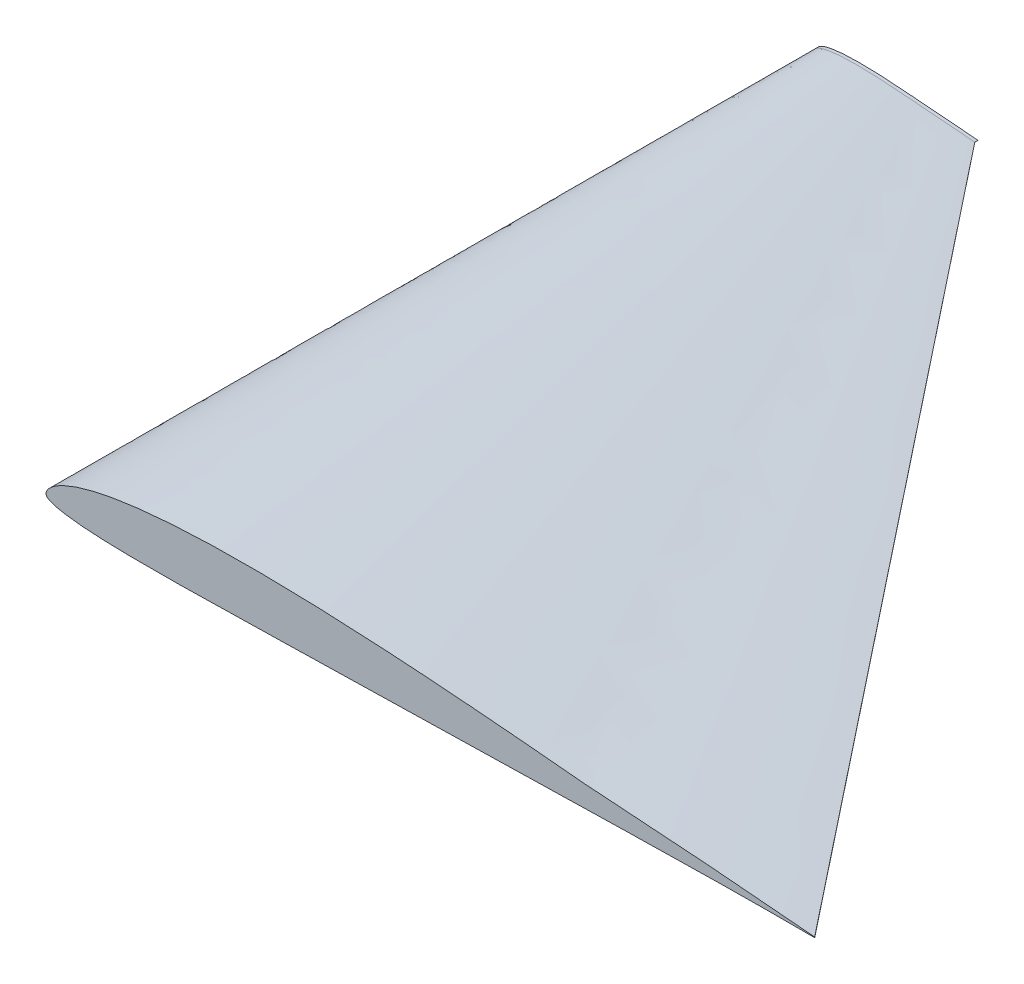
SolidWorks part; units mm, degrees
ref_plane "Front Plane" through (0, 0, 0) normal (0, 0, 1) x (1, 0, 0)
ref_plane "Top Plane" through (0, 0, 0) normal (0, 1, 0) x (1, 0, 0)
ref_plane "Right Plane" through (0, 0, 0) normal (1, 0, 0) x (0, 0, -1)
curve "Curve1"
  spline degree 3 poles (25.4, 0.0107, 0) (25.3506, 0.0152, 0) (25.2009, 0.0289, 0) (24.9376, 0.0531, 0) (24.6076, 0.082, 0) (24.2616, 0.1124, 0) (23.9125, 0.1431, 0) (23.5625, 0.1725, 0) (23.212, 0.2019, 0) (22.8613, 0.2307, 0) (22.5105, 0.2591, 0) (22.1596, 0.2869, 0) (21.8089, 0.314, 0) (21.4582, 0.3409, 0) (21.1077, 0.367, 0) (20.7573, 0.3928, 0) (20.407, 0.4182, 0) (20.0568, 0.4428, 0) (19.7068, 0.4673, 0) (19.3568, 0.4911, 0) (19.0069, 0.5145, 0) (18.6571, 0.5374, 0) (18.3335, 0.5583, 0) (18.0818, 0.5739, 0) (17.9246, 0.5843, 0) (17.8356, 0.5888, 0) (17.7472, 0.5983, 0) (17.5613, 0.6156, 0) (17.278, 0.6431, 0) (16.98, 0.6709, 0) (16.7137, 0.6956, 0) (16.4751, 0.7176, 0) (16.176, 0.7447, 0) (15.8267, 0.776, 0) (15.4701, 0.8073, 0) (15.1145, 0.838, 0) (14.7793, 0.8663, 0) (14.4495, 0.8936, 0) (14.1621, 0.9169, 0) (13.925, 0.9358, 0) (13.6642, 0.9563, 0) (13.3619, 0.9794, 0) (13.0103, 1.0056, 0) (12.659, 1.031, 0) (12.3077, 1.0554, 0) (11.9565, 1.0789, 0) (11.6054, 1.1014, 0) (11.2544, 1.1228, 0) (10.9034, 1.1432, 0) (10.5525, 1.1624, 0) (10.2016, 1.1803, 0) (9.8507, 1.197, 0) (9.5, 1.2123, 0) (9.1492, 1.2263, 0) (8.7986, 1.2386, 0) (8.448, 1.2494, 0) (8.0977, 1.2585, 0) (7.7474, 1.2658, 0) (7.3974, 1.2711, 0) (7.0475, 1.2745, 0) (6.6979, 1.2756, 0) (6.3485, 1.2744, 0) (5.9995, 1.2706, 0) (5.6509, 1.2642, 0) (5.3028, 1.2548, 0) (4.9554, 1.2422, 0) (4.6087, 1.2261, 0) (4.2629, 1.2062, 0) (3.9183, 1.1823, 0) (3.5751, 1.1536, 0) (3.2336, 1.12, 0) (2.8944, 1.0807, 0) (2.5581, 1.0351, 0) (2.2254, 0.9824, 0) (1.8975, 0.9214, 0) (1.5762, 0.8511, 0) (1.2643, 0.7698, 0) (0.9677, 0.6771, 0) (0.6972, 0.5737, 0) (0.4689, 0.4653, 0) (0.2948, 0.361, 0) (0.1747, 0.2696, 0) (0.0967, 0.1939, 0) (0.0471, 0.1311, 0) (0.0171, 0.0777, 0) (0.0019, 0.0319, 0) (-0.0016, -0.0085, 0) (0.0071, -0.0466, 0) (0.0322, -0.0832, 0) (0.0764, -0.1158, 0) (0.1405, -0.1489, 0) (0.2348, -0.1846, 0) (0.3747, -0.2244, 0) (0.5727, -0.265, 0) (0.8268, -0.3029, 0) (1.1218, -0.3343, 0) (1.4394, -0.3584, 0) (1.7684, -0.3763, 0) (2.1036, -0.389, 0) (2.4428, -0.3976, 0) (2.7846, -0.4031, 0) (3.1285, -0.4061, 0) (3.4739, -0.407, 0) (3.8205, -0.4061, 0) (4.168, -0.4035, 0) (4.5164, -0.3997, 0) (4.8654, -0.3948, 0) (5.2151, -0.389, 0) (5.5654, -0.3825, 0) (5.9165, -0.3755, 0) (6.2684, -0.368, 0) (6.621, -0.3604, 0) (6.9745, -0.3524, 0) (7.3287, -0.3442, 0) (7.6835, -0.336, 0) (8.039, -0.3276, 0) (8.3948, -0.3192, 0) (8.7511, -0.3108, 0) (9.1077, -0.3024, 0) (9.4646, -0.2939, 0) (9.8219, -0.2855, 0) (10.1795, -0.2771, 0) (10.5373, -0.2687, 0) (10.8952, -0.2603, 0) (11.2527, -0.252, 0) (11.6101, -0.2438, 0) (11.9672, -0.2355, 0) (12.3241, -0.2274, 0) (12.6807, -0.2193, 0) (13.0371, -0.2114, 0) (13.3934, -0.2033, 0) (13.6949, -0.1966, 0) (13.9592, -0.1908, 0) (14.1921, -0.1856, 0) (14.4749, -0.1792, 0) (14.7878, -0.1723, 0) (15.131, -0.1647, 0) (15.4754, -0.1569, 0) (15.8234, -0.1492, 0) (16.1349, -0.1423, 0) (16.4075, -0.1363, 0) (16.6379, -0.1313, 0) (16.9029, -0.1255, 0) (17.2072, -0.1189, 0) (17.4885, -0.1128, 0) (17.6791, -0.1088, 0) (17.7715, -0.1068, 0) (17.8501, -0.1053, 0) (18.0096, -0.1018, 0) (18.269, -0.0964, 0) (18.61, -0.0893, 0) (18.9621, -0.082, 0) (19.3141, -0.0749, 0) (19.666, -0.0678, 0) (20.0179, -0.0609, 0) (20.3698, -0.054, 0) (20.7219, -0.0473, 0) (21.074, -0.0408, 0) (21.4262, -0.0348, 0) (21.7784, -0.0292, 0) (22.1308, -0.0242, 0) (22.4832, -0.0197, 0) (22.8357, -0.0157, 0) (23.1883, -0.0125, 0) (23.5408, -0.0098, 0) (23.8935, -0.008, 0) (24.246, -0.0071, 0) (24.5963, -0.007, 0) (24.9308, -0.0084, 0) (25.198, -0.0096, 0) (25.3499, -0.0104, 0) (25.4, -0.0107, 0) knots 0 0 0 0 0.002901 0.008799 0.015478 0.022288 0.029131 0.035985 0.042847 0.049714 0.056581 0.063448 0.070313 0.077171 0.084031 0.090885 0.097737 0.104584 0.111432 0.118275 0.125116 0.131954 0.138793 0.144098 0.146709 0.148014 0.149313 0.151911 0.158945 0.165974 0.169425 0.174599 0.18 0.186998 0.195126 0.200949 0.20789 0.214818 0.220317 0.224762 0.228741 0.235631 0.242503 0.249376 0.256249 0.263115 0.269975 0.276837 0.283698 0.290553 0.297409 0.304262 0.311112 0.317958 0.324805 0.331647 0.338484 0.345319 0.352149 0.358974 0.365797 0.372613 0.37942 0.386225 0.393018 0.399801 0.406576 0.413331 0.420073 0.426793 0.433487 0.440154 0.446776 0.453353 0.459862 0.466294 0.472602 0.478718 0.484477 0.489534 0.493496 0.496331 0.498346 0.499841 0.500999 0.501915 0.502649 0.503345 0.504158 0.505185 0.506526 0.508376 0.511074 0.515031 0.520197 0.526109 0.532386 0.538838 0.545393 0.552019 0.558693 0.565404 0.572145 0.578909 0.585689 0.592488 0.599298 0.60612 0.612956 0.619809 0.626673 0.633554 0.640451 0.647364 0.654291 0.661227 0.668172 0.675126 0.682086 0.689049 0.69602 0.703 0.709987 0.71697 0.723948 0.73092 0.73789 0.744856 0.751814 0.758769 0.765721 0.77267 0.776424 0.78119 0.786305 0.792978 0.79951 0.806399 0.81314 0.819881 0.824633 0.829103 0.833367 0.840145 0.84692 0.849831 0.851305 0.852333 0.85443 0.860642 0.867519 0.87439 0.881257 0.888123 0.894989 0.901857 0.908727 0.915597 0.922469 0.929344 0.936217 0.943092 0.949972 0.956848 0.963729 0.970609 0.97749 0.984361 0.991109 0.997067 1 1 1 1
sketch "Sketch2" plane through (0, 0, 0) normal (0, 0, 1) x (1, 0, 0)
  line L0 (64.7182, -2.4991) -> (64.7182, -2.5635)
  line L1 (127, 0.0536) -> (127, -0.0536)
  line L2 (0, 0) -> (127, 0.0536) construction
  spline S1 degree 3 poles (609.6, 0.2573) (608.4153, 0.3652) (604.8219, 0.6927) (598.502, 1.2752) (590.5825, 1.9674) (582.2775, 2.6983) (573.9006, 3.4339) (565.4998, 4.1403) (557.089, 4.8463) (548.6715, 5.5358) (540.2515, 6.218) (531.8311, 6.8852) (523.413, 7.5348) (514.9974, 8.1818) (506.5852, 8.8084) (498.1747, 9.4281) (489.7686, 10.036) (481.3637, 10.627) (472.9627, 11.2149) (464.5629, 11.7866) (456.1664, 12.3471) (447.7708, 12.8983) (440.0032, 13.3997) (433.9644, 13.7741) (430.1915, 14.0231) (428.0555, 14.1319) (425.9338, 14.3593) (421.4712, 14.7735) (414.6712, 15.4343) (407.5204, 16.1015) (401.1285, 16.6942) (395.4014, 17.222) (388.2248, 17.8734) (379.8411, 18.6251) (371.2834, 19.3759) (362.7481, 20.1109) (354.702, 20.791) (346.7874, 21.4473) (339.8916, 22.0057) (334.2002, 22.4585) (327.9397, 22.9514) (320.686, 23.506) (312.248, 24.1341) (303.8155, 24.7432) (292.5775, 25.5244) (281.3407, 26.2607) (270.1062, 26.9482) (261.6823, 27.4364) (250.4535, 28.0507) (239.2258, 28.6059) (227.9988, 29.096) (219.5815, 29.4314) (211.1661, 29.7272) (202.7531, 29.9856) (194.3438, 30.2035) (185.9386, 30.3795) (177.5376, 30.5072) (169.1408, 30.5885) (160.7491, 30.6149) (152.3646, 30.5852) (143.9885, 30.4949) (135.6226, 30.341) (127.2682, 30.115) (118.9286, 29.8125) (110.6079, 29.4273) (102.3088, 28.9496) (94.0382, 28.3746) (85.8017, 27.6874) (77.6067, 26.8808) (69.4667, 25.9361) (61.3935, 24.8424) (53.4108, 23.5771) (45.5411, 22.1146) (37.8288, 20.426) (30.344, 18.4761) (23.2242, 16.2498) (16.7336, 13.7685) (11.2526, 11.1662) (7.0744, 8.6642) (4.192, 6.4716) (2.3207, 4.6541) (1.1306, 3.147) (0.4097, 1.8653) (0.0445, 0.7644) (-0.0394, -0.2051) (0.1701, -1.1192) (0.7717, -1.9972) (1.8329, -2.7786) (3.3717, -3.5735) (5.6341, -4.4311) (8.992, -5.3852) (13.7441, -6.3602) (19.844, -7.2691) (26.9221, -8.0223) (34.5451, -8.6019) (42.4418, -9.0313) (50.4869, -9.3361) (58.6261, -9.543) (66.8307, -9.6749) (75.0831, -9.7467) (83.3728, -9.7692) (91.6908, -9.7458) (100.0329, -9.6848) (108.3931, -9.5935) (116.7701, -9.4746) (125.1618, -9.3356) (133.5708, -9.1799) (141.9971, -9.0125) (150.4416, -8.8321) (158.9043, -8.6491) (167.3869, -8.4567) (175.8879, -8.2608) (187.2521, -7.9967) (198.6327, -7.7272) (210.0269, -7.4583) (218.5851, -7.2569) (227.1506, -7.0539) (235.7244, -6.8527) (244.3077, -6.6496) (252.896, -6.449) (261.4836, -6.2483) (270.0654, -6.0486) (278.6417, -5.8521) (287.2128, -5.6526) (295.7783, -5.4585) (304.3375, -5.264) (312.891, -5.0728) (321.4408, -4.88) (328.6786, -4.7192) (337.1174, -4.5324) (345.4426, -4.3447) (354.9071, -4.135) (363.1446, -3.9522) (371.4102, -3.7664) (379.7615, -3.5814) (387.2366, -3.4158) (393.7811, -3.2715) (399.3097, -3.1512) (405.6693, -3.0117) (412.9735, -2.8543) (419.723, -2.7081) (424.2983, -2.6117) (426.5172, -2.5634) (428.4027, -2.5274) (432.2303, -2.443) (438.4564, -2.3133) (446.6397, -2.1424) (455.0912, -1.9684) (463.5382, -1.7984) (471.983, -1.6281) (480.4288, -1.4625) (488.876, -1.2962) (497.3253, -1.1358) (505.7757, -0.9782) (514.2284, -0.8363) (525.5014, -0.6571) (536.7782, -0.5043) (548.0561, -0.376) (556.518, -0.299) (564.9803, -0.2347) (573.4446, -0.1921) (581.9048, -0.1708) (590.3111, -0.1673) (598.3385, -0.2004) (604.7515, -0.2296) (608.3973, -0.2504) (609.6, -0.2573) knots 0 0 0 0 0.002901 0.008799 0.015478 0.022288 0.029131 0.035985 0.042847 0.049714 0.056581 0.063448 0.070313 0.077171 0.084031 0.090885 0.097737 0.104584 0.111432 0.118275 0.125116 0.131954 0.138793 0.144098 0.146709 0.148014 0.149313 0.151911 0.158945 0.165974 0.169425 0.174599 0.18 0.186998 0.195126 0.200949 0.20789 0.214818 0.220317 0.224762 0.228741 0.235631 0.242503 0.249376 0.256249 0.269975 0.276837 0.283698 0.290553 0.304262 0.311112 0.317958 0.324805 0.331647 0.338484 0.345319 0.352149 0.358974 0.365797 0.372613 0.37942 0.386225 0.393018 0.399801 0.406576 0.413331 0.420073 0.426793 0.433487 0.440154 0.446776 0.453353 0.459862 0.466294 0.472602 0.478718 0.484477 0.489534 0.493496 0.496331 0.498346 0.499841 0.500999 0.501915 0.502649 0.503345 0.504158 0.505185 0.506526 0.508376 0.511074 0.515031 0.520197 0.526109 0.532386 0.538838 0.545393 0.552019 0.558693 0.565404 0.572145 0.578909 0.585689 0.592488 0.599298 0.60612 0.612956 0.619809 0.626673 0.633554 0.640451 0.647364 0.654291 0.668172 0.675126 0.682086 0.689049 0.69602 0.703 0.709987 0.71697 0.723948 0.73092 0.73789 0.744856 0.751814 0.758769 0.765721 0.77267 0.776424 0.786305 0.792978 0.79951 0.806399 0.81314 0.819881 0.824633 0.829103 0.833367 0.840145 0.84692 0.849831 0.851305 0.852333 0.85443 0.860642 0.867519 0.87439 0.881257 0.888123 0.894989 0.901857 0.908727 0.915597 0.922469 0.929344 0.943092 0.949972 0.956848 0.963729 0.970609 0.97749 0.984361 0.991109 0.997067 1 1 1 1
  spline S2 degree 3 poles (127, 0.0536) (126.7532, 0.0761) (126.0046, 0.1443) (124.6879, 0.2657) (123.038, 0.4099) (121.3078, 0.5622) (119.5626, 0.7154) (117.8125, 0.8626) (116.0602, 1.0096) (114.3066, 1.1533) (112.5524, 1.2954) (110.7981, 1.4344) (109.0444, 1.5698) (107.2911, 1.7045) (105.5386, 1.8351) (103.7864, 1.9642) (102.0351, 2.0908) (100.2841, 2.214) (98.5339, 2.3364) (96.7839, 2.4555) (95.0347, 2.5723) (93.2856, 2.6871) (91.6673, 2.7916) (90.4092, 2.8696) (89.6232, 2.9215) (89.1782, 2.9441) (88.7362, 2.9915) (87.8065, 3.0778) (86.3898, 3.2155) (84.9001, 3.3545) (83.5684, 3.478) (82.3753, 3.5879) (80.8802, 3.7236) (79.1336, 3.8802) (77.3507, 4.0366) (75.5725, 4.1898) (73.8963, 4.3315) (72.2474, 4.4682) (70.8107, 4.5845) (69.625, 4.6789) (68.3208, 4.7815) (66.8096, 4.8971) (65.0517, 5.0279) (63.2949, 5.1548) (60.9536, 5.3176) (58.6126, 5.471) (56.2721, 5.6142) (54.5172, 5.7159) (52.1778, 5.8439) (49.8387, 5.9596) (47.4998, 6.0617) (45.7461, 6.1315) (43.9929, 6.1932) (42.2402, 6.247) (40.4883, 6.2924) (38.7372, 6.3291) (36.987, 6.3557) (35.2377, 6.3726) (33.4894, 6.3781) (31.7426, 6.3719) (29.9976, 6.3531) (28.2547, 6.321) (26.5142, 6.274) (24.7768, 6.2109) (23.0433, 6.1307) (21.3143, 6.0312) (19.5913, 5.9114) (17.8753, 5.7682) (16.1681, 5.6002) (14.4722, 5.4034) (12.7903, 5.1755) (11.1272, 4.9119) (9.4877, 4.6072) (7.881, 4.2554) (6.3217, 3.8492) (4.8384, 3.3854) (3.4862, 2.8684) (2.3443, 2.3263) (1.4738, 1.805) (0.8733, 1.3482) (0.4835, 0.9696) (0.2355, 0.6556) (0.0854, 0.3886) (0.0093, 0.1593) (-0.0082, -0.0427) (0.0354, -0.2332) (0.1608, -0.4161) (0.3818, -0.5789) (0.7024, -0.7445) (1.1738, -0.9231) (1.8733, -1.1219) (2.8634, -1.3251) (4.1342, -1.5144) (5.6088, -1.6713) (7.1969, -1.7921) (8.842, -1.8815) (10.5181, -1.945) (12.2138, -1.9881) (13.9231, -2.0156) (15.6423, -2.0306) (17.3693, -2.0352) (19.1023, -2.0304) (20.8402, -2.0177) (22.5819, -1.9987) (24.3271, -1.9739) (26.0754, -1.9449) (27.8272, -1.9125) (29.5827, -1.8776) (31.342, -1.84) (33.1051, -1.8019) (34.8723, -1.7618) (36.6433, -1.721) (39.0109, -1.666) (41.3818, -1.6098) (43.7556, -1.5538) (45.5386, -1.5118) (47.323, -1.4696) (49.1093, -1.4276) (50.8974, -1.3853) (52.6867, -1.3435) (54.4758, -1.3017) (56.2636, -1.2601) (58.0503, -1.2192) (59.836, -1.1776) (61.6205, -1.1372) (63.4036, -1.0967) (65.1856, -1.0568) (66.9668, -1.0167) (68.4747, -0.9832) (70.2328, -0.9443) (71.9672, -0.9051) (73.939, -0.8615) (75.6551, -0.8234) (77.3771, -0.7847) (79.117, -0.7461) (80.6743, -0.7116) (82.0377, -0.6816) (83.1895, -0.6565) (84.5144, -0.6274) (86.0361, -0.5947) (87.4423, -0.5642) (88.3955, -0.5441) (88.8577, -0.534) (89.2506, -0.5265) (90.048, -0.509) (91.3451, -0.4819) (93.0499, -0.4463) (94.8107, -0.4101) (96.5705, -0.3747) (98.3298, -0.3392) (100.0893, -0.3047) (101.8492, -0.27) (103.6094, -0.2366) (105.3699, -0.2038) (107.1309, -0.1742) (109.4795, -0.1369) (111.8288, -0.1051) (114.1784, -0.0783) (115.9413, -0.0623) (117.7042, -0.0489) (119.4676, -0.04) (121.2302, -0.0356) (122.9815, -0.0349) (124.6538, -0.0418) (125.9899, -0.0478) (126.7494, -0.0522) (127, -0.0536) knots 0 0 0 0 0.002901 0.008799 0.015478 0.022288 0.029131 0.035985 0.042847 0.049714 0.056581 0.063448 0.070313 0.077171 0.084031 0.090885 0.097737 0.104584 0.111432 0.118275 0.125116 0.131954 0.138793 0.144098 0.146709 0.148014 0.149313 0.151911 0.158945 0.165974 0.169425 0.174599 0.18 0.186998 0.195126 0.200949 0.20789 0.214818 0.220317 0.224762 0.228741 0.235631 0.242503 0.249376 0.256249 0.269975 0.276837 0.283698 0.290553 0.304262 0.311112 0.317958 0.324805 0.331647 0.338484 0.345319 0.352149 0.358974 0.365797 0.372613 0.37942 0.386225 0.393018 0.399801 0.406576 0.413331 0.420073 0.426793 0.433487 0.440154 0.446776 0.453353 0.459862 0.466294 0.472602 0.478718 0.484477 0.489534 0.493496 0.496331 0.498346 0.499841 0.500999 0.501915 0.502649 0.503345 0.504158 0.505185 0.506526 0.508376 0.511074 0.515031 0.520197 0.526109 0.532386 0.538838 0.545393 0.552019 0.558693 0.565404 0.572145 0.578909 0.585689 0.592488 0.599298 0.60612 0.612956 0.619809 0.626673 0.633554 0.640451 0.647364 0.654291 0.668172 0.675126 0.682086 0.689049 0.69602 0.703 0.709987 0.71697 0.723948 0.73092 0.73789 0.744856 0.751814 0.758769 0.765721 0.77267 0.776424 0.786305 0.792978 0.79951 0.806399 0.81314 0.819881 0.824633 0.829103 0.833367 0.840145 0.84692 0.849831 0.851305 0.852333 0.85443 0.860642 0.867519 0.87439 0.881257 0.888123 0.894989 0.901857 0.908727 0.915597 0.922469 0.929344 0.943092 0.949972 0.956848 0.963729 0.970609 0.97749 0.984361 0.991109 0.997067 1 1 1 1
extrude "Boss-Extrude1" add sketch "Sketch2" along normal mid plane 2.54
ref_plane "Plane1" through (0, 0, 610.87) normal (0, 0, 1) x (1, 0, 0)
sketch "Sketch3" plane through (0, 0, 610.87) normal (0, 0, 1) x (1, 0, 0)
  line L0 (609.6, 0.2573) -> (609.6, -0.2573)
  line L1 (0, 0) -> (609.6, 0.2573) construction
  spline S0 degree 3 poles (1038.8078, -2921.9881) (1066.9783, -26.4878) (833.4176, -20.3761) (598.502, 1.2752) (590.5825, 1.9674) (582.2775, 2.6983) (573.9006, 3.4339) (565.4998, 4.1403) (557.089, 4.8463) (548.6715, 5.5358) (540.2515, 6.218) (531.8311, 6.8852) (523.413, 7.5348) (514.9974, 8.1818) (506.5852, 8.8084) (498.1747, 9.4281) (489.7686, 10.036) (481.3637, 10.627) (472.9627, 11.2149) (464.5629, 11.7866) (456.1664, 12.3471) (447.7708, 12.8983) (440.0032, 13.3997) (433.9644, 13.7741) (430.1915, 14.0231) (428.0555, 14.1319) (425.9338, 14.3593) (421.4712, 14.7735) (414.6712, 15.4343) (407.5204, 16.1015) (401.1285, 16.6942) (395.4014, 17.222) (388.2248, 17.8734) (379.8411, 18.6251) (371.2834, 19.3759) (362.7481, 20.1109) (354.702, 20.791) (346.7874, 21.4473) (339.8916, 22.0057) (334.2002, 22.4585) (327.9397, 22.9514) (320.686, 23.506) (312.248, 24.1341) (303.8155, 24.7432) (292.5775, 25.5244) (281.3407, 26.2607) (270.1062, 26.9482) (261.6823, 27.4364) (250.4535, 28.0507) (239.2258, 28.6059) (227.9988, 29.096) (219.5815, 29.4314) (211.1661, 29.7272) (202.7531, 29.9856) (194.3438, 30.2035) (185.9386, 30.3795) (177.5376, 30.5072) (169.1408, 30.5885) (160.7491, 30.6149) (152.3646, 30.5852) (143.9885, 30.4949) (135.6226, 30.341) (127.2682, 30.115) (118.9286, 29.8125) (110.6079, 29.4273) (102.3088, 28.9496) (94.0382, 28.3746) (85.8017, 27.6874) (77.6067, 26.8808) (69.4667, 25.9361) (61.3935, 24.8424) (53.4108, 23.5771) (45.5411, 22.1146) (37.8288, 20.426) (30.344, 18.4761) (23.2242, 16.2498) (16.7336, 13.7685) (11.2526, 11.1662) (7.0744, 8.6642) (4.192, 6.4716) (2.3207, 4.6541) (1.1306, 3.147) (0.4097, 1.8653) (0.0445, 0.7644) (-0.0394, -0.2051) (0.1701, -1.1192) (0.7717, -1.9972) (1.8329, -2.7786) (3.3717, -3.5735) (5.6341, -4.4311) (8.992, -5.3852) (13.7441, -6.3602) (19.844, -7.2691) (26.9221, -8.0223) (34.5451, -8.6019) (42.4418, -9.0313) (50.4869, -9.3361) (58.6261, -9.543) (66.8307, -9.6749) (75.0831, -9.7467) (83.3728, -9.7692) (91.6908, -9.7458) (100.0329, -9.6848) (108.3931, -9.5935) (116.7701, -9.4746) (125.1618, -9.3356) (133.5708, -9.1799) (141.9971, -9.0125) (150.4416, -8.8321) (158.9043, -8.6491) (167.3869, -8.4567) (175.8879, -8.2608) (187.2521, -7.9967) (198.6327, -7.7272) (210.0269, -7.4583) (218.5851, -7.2569) (227.1506, -7.0539) (235.7244, -6.8527) (244.3077, -6.6496) (252.896, -6.449) (261.4836, -6.2483) (270.0654, -6.0486) (278.6417, -5.8521) (287.2128, -5.6526) (295.7783, -5.4585) (304.3375, -5.264) (312.891, -5.0728) (321.4408, -4.88) (328.6786, -4.7192) (337.1174, -4.5324) (345.4426, -4.3447) (354.9071, -4.135) (363.1446, -3.9522) (371.4102, -3.7664) (379.7615, -3.5814) (387.2366, -3.4158) (393.7811, -3.2715) (399.3097, -3.1512) (405.6693, -3.0117) (412.9735, -2.8543) (419.723, -2.7081) (424.2983, -2.6117) (426.5172, -2.5634) (428.4027, -2.5274) (432.2303, -2.443) (438.4564, -2.3133) (446.6397, -2.1424) (455.0912, -1.9684) (463.5382, -1.7984) (471.983, -1.6281) (480.4288, -1.4625) (488.876, -1.2962) (497.3253, -1.1358) (505.7757, -0.9782) (514.2284, -0.8363) (525.5014, -0.6571) (536.7782, -0.5043) (548.0561, -0.376) (556.518, -0.299) (564.9803, -0.2347) (573.4446, -0.1921) (581.9048, -0.1708) (590.3111, -0.1673) (598.3385, -0.2004) (826.9233, -1.2405) (1052.6631, -18.3792) (1290.0483, 2876.6987) knots -0.559833 -0.559833 -0.559833 -0.559833 0.002901 0.008799 0.015478 0.022288 0.029131 0.035985 0.042847 0.049714 0.056581 0.063448 0.070313 0.077171 0.084031 0.090885 0.097737 0.104584 0.111432 0.118275 0.125116 0.131954 0.138793 0.144098 0.146709 0.148014 0.149313 0.151911 0.158945 0.165974 0.169425 0.174599 0.18 0.186998 0.195126 0.200949 0.20789 0.214818 0.220317 0.224762 0.228741 0.235631 0.242503 0.249376 0.256249 0.269975 0.276837 0.283698 0.290553 0.304262 0.311112 0.317958 0.324805 0.331647 0.338484 0.345319 0.352149 0.358974 0.365797 0.372613 0.37942 0.386225 0.393018 0.399801 0.406576 0.413331 0.420073 0.426793 0.433487 0.440154 0.446776 0.453353 0.459862 0.466294 0.472602 0.478718 0.484477 0.489534 0.493496 0.496331 0.498346 0.499841 0.500999 0.501915 0.502649 0.503345 0.504158 0.505185 0.506526 0.508376 0.511074 0.515031 0.520197 0.526109 0.532386 0.538838 0.545393 0.552019 0.558693 0.565404 0.572145 0.578909 0.585689 0.592488 0.599298 0.60612 0.612956 0.619809 0.626673 0.633554 0.640451 0.647364 0.654291 0.668172 0.675126 0.682086 0.689049 0.69602 0.703 0.709987 0.71697 0.723948 0.73092 0.73789 0.744856 0.751814 0.758769 0.765721 0.77267 0.776424 0.786305 0.792978 0.79951 0.806399 0.81314 0.819881 0.824633 0.829103 0.833367 0.840145 0.84692 0.849831 0.851305 0.852333 0.85443 0.860642 0.867519 0.87439 0.881257 0.888123 0.894989 0.901857 0.908727 0.915597 0.922469 0.929344 0.943092 0.949972 0.956848 0.963729 0.970609 0.97749 0.984361 0.991109 0.997067 1.541811 1.541811 1.541811 1.541811 only from (609.6, 0.2573) to (609.6, -0.2573) construction
  spline S1 degree 3 poles (609.6, 0.2573) (608.4153, 0.3652) (604.8219, 0.6927) (598.502, 1.2752) (590.5825, 1.9674) (582.2775, 2.6983) (573.9006, 3.4339) (565.4998, 4.1403) (557.089, 4.8463) (548.6715, 5.5358) (540.2515, 6.218) (531.8311, 6.8852) (523.413, 7.5348) (514.9974, 8.1818) (506.5852, 8.8084) (498.1747, 9.4281) (489.7686, 10.036) (481.3637, 10.627) (472.9627, 11.2149) (464.5629, 11.7866) (456.1664, 12.3471) (447.7708, 12.8983) (440.0032, 13.3997) (433.9644, 13.7741) (430.1915, 14.0231) (428.0555, 14.1319) (425.9338, 14.3593) (421.4712, 14.7735) (414.6712, 15.4343) (407.5204, 16.1015) (401.1285, 16.6942) (395.4014, 17.222) (388.2248, 17.8734) (379.8411, 18.6251) (371.2834, 19.3759) (362.7481, 20.1109) (354.702, 20.791) (346.7874, 21.4473) (339.8916, 22.0057) (334.2002, 22.4585) (327.9397, 22.9514) (320.686, 23.506) (312.248, 24.1341) (303.8155, 24.7432) (292.5775, 25.5244) (281.3407, 26.2607) (270.1062, 26.9482) (261.6823, 27.4364) (250.4535, 28.0507) (239.2258, 28.6059) (227.9988, 29.096) (219.5815, 29.4314) (211.1661, 29.7272) (202.7531, 29.9856) (194.3438, 30.2035) (185.9386, 30.3795) (177.5376, 30.5072) (169.1408, 30.5885) (160.7491, 30.6149) (152.3646, 30.5852) (143.9885, 30.4949) (135.6226, 30.341) (127.2682, 30.115) (118.9286, 29.8125) (110.6079, 29.4273) (102.3088, 28.9496) (94.0382, 28.3746) (85.8017, 27.6874) (77.6067, 26.8808) (69.4667, 25.9361) (61.3935, 24.8424) (53.4108, 23.5771) (45.5411, 22.1146) (37.8288, 20.426) (30.344, 18.4761) (23.2242, 16.2498) (16.7336, 13.7685) (11.2526, 11.1662) (7.0744, 8.6642) (4.192, 6.4716) (2.3207, 4.6541) (1.1306, 3.147) (0.4097, 1.8653) (0.0445, 0.7644) (-0.0394, -0.2051) (0.1701, -1.1192) (0.7717, -1.9972) (1.8329, -2.7786) (3.3717, -3.5735) (5.6341, -4.4311) (8.992, -5.3852) (13.7441, -6.3602) (19.844, -7.2691) (26.9221, -8.0223) (34.5451, -8.6019) (42.4418, -9.0313) (50.4869, -9.3361) (58.6261, -9.543) (66.8307, -9.6749) (75.0831, -9.7467) (83.3728, -9.7692) (91.6908, -9.7458) (100.0329, -9.6848) (108.3931, -9.5935) (116.7701, -9.4746) (125.1618, -9.3356) (133.5708, -9.1799) (141.9971, -9.0125) (150.4416, -8.8321) (158.9043, -8.6491) (167.3869, -8.4567) (175.8879, -8.2608) (187.2521, -7.9967) (198.6327, -7.7272) (210.0269, -7.4583) (218.5851, -7.2569) (227.1506, -7.0539) (235.7244, -6.8527) (244.3077, -6.6496) (252.896, -6.449) (261.4836, -6.2483) (270.0654, -6.0486) (278.6417, -5.8521) (287.2128, -5.6526) (295.7783, -5.4585) (304.3375, -5.264) (312.891, -5.0728) (321.4408, -4.88) (328.6786, -4.7192) (337.1174, -4.5324) (345.4426, -4.3447) (354.9071, -4.135) (363.1446, -3.9522) (371.4102, -3.7664) (379.7615, -3.5814) (387.2366, -3.4158) (393.7811, -3.2715) (399.3097, -3.1512) (405.6693, -3.0117) (412.9735, -2.8543) (419.723, -2.7081) (424.2983, -2.6117) (426.5172, -2.5634) (428.4027, -2.5274) (432.2303, -2.443) (438.4564, -2.3133) (446.6397, -2.1424) (455.0912, -1.9684) (463.5382, -1.7984) (471.983, -1.6281) (480.4288, -1.4625) (488.876, -1.2962) (497.3253, -1.1358) (505.7757, -0.9782) (514.2284, -0.8363) (525.5014, -0.6571) (536.7782, -0.5043) (548.0561, -0.376) (556.518, -0.299) (564.9803, -0.2347) (573.4446, -0.1921) (581.9048, -0.1708) (590.3111, -0.1673) (598.3385, -0.2004) (604.7515, -0.2296) (608.3973, -0.2504) (609.6, -0.2573) knots 0 0 0 0 0.002901 0.008799 0.015478 0.022288 0.029131 0.035985 0.042847 0.049714 0.056581 0.063448 0.070313 0.077171 0.084031 0.090885 0.097737 0.104584 0.111432 0.118275 0.125116 0.131954 0.138793 0.144098 0.146709 0.148014 0.149313 0.151911 0.158945 0.165974 0.169425 0.174599 0.18 0.186998 0.195126 0.200949 0.20789 0.214818 0.220317 0.224762 0.228741 0.235631 0.242503 0.249376 0.256249 0.269975 0.276837 0.283698 0.290553 0.304262 0.311112 0.317958 0.324805 0.331647 0.338484 0.345319 0.352149 0.358974 0.365797 0.372613 0.37942 0.386225 0.393018 0.399801 0.406576 0.413331 0.420073 0.426793 0.433487 0.440154 0.446776 0.453353 0.459862 0.466294 0.472602 0.478718 0.484477 0.489534 0.493496 0.496331 0.498346 0.499841 0.500999 0.501915 0.502649 0.503345 0.504158 0.505185 0.506526 0.508376 0.511074 0.515031 0.520197 0.526109 0.532386 0.538838 0.545393 0.552019 0.558693 0.565404 0.572145 0.578909 0.585689 0.592488 0.599298 0.60612 0.612956 0.619809 0.626673 0.633554 0.640451 0.647364 0.654291 0.668172 0.675126 0.682086 0.689049 0.69602 0.703 0.709987 0.71697 0.723948 0.73092 0.73789 0.744856 0.751814 0.758769 0.765721 0.77267 0.776424 0.786305 0.792978 0.79951 0.806399 0.81314 0.819881 0.824633 0.829103 0.833367 0.840145 0.84692 0.849831 0.851305 0.852333 0.85443 0.860642 0.867519 0.87439 0.881257 0.888123 0.894989 0.901857 0.908727 0.915597 0.922469 0.929344 0.943092 0.949972 0.956848 0.963729 0.970609 0.97749 0.984361 0.991109 0.997067 1 1 1 1
loft "Loft4" add profiles "Sketch3" section face at (127, 0.0268, 1.27) section "Sketch3"
